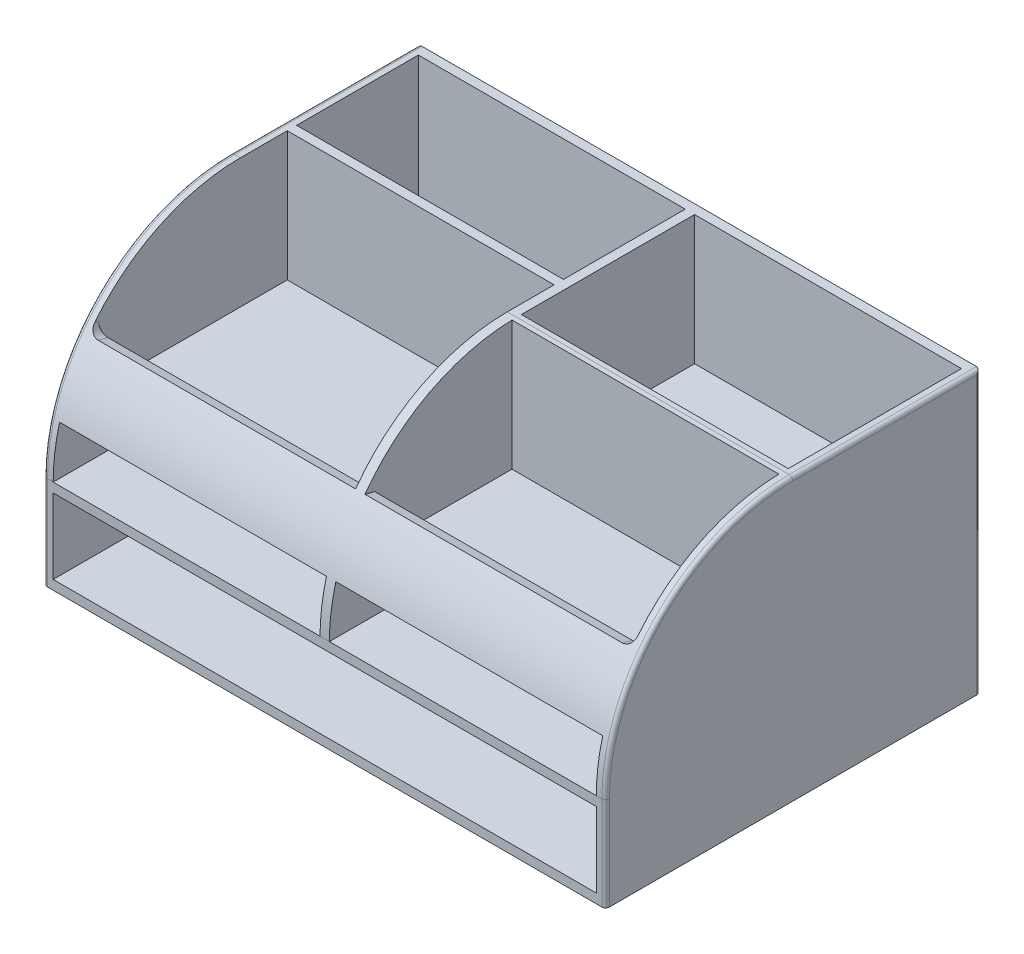
SolidWorks part; units mm, degrees
ref_plane "Front Plane" through (0, 0, 0) normal (0, 0, 1) x (1, 0, 0)
ref_plane "Top Plane" through (0, 0, 0) normal (0, 1, 0) x (1, 0, 0)
ref_plane "Right Plane" through (0, 0, 0) normal (1, 0, 0) x (0, 0, -1)
sketch "Sketch1" plane through (0, 0, 0) normal (1, 0, 0) x (0, 0, -1)
  line L0 (-96.9697, -62.8788) -> (103.0303, -62.8788)
  line L1 (103.0303, -62.8788) -> (103.0303, 87.1212)
  line L2 (103.0303, 87.1212) -> (3.0303, 87.1212)
  line L3 (-96.9697, -12.8788) -> (-96.9697, -62.8788)
  arc A1 (3.0303, 87.1212) -> (-96.9697, -12.8788) centre (3.0303, -12.8788) ccw
  dimension "D3" = 100
  dimension "D1" = 200
  dimension "D2" = 150
extrude "Boss-Extrude1" add sketch "Sketch1" against normal blind 300
sketch "Sketch2" plane through (0, 87.1212, 0) normal (0, 1, 0) x (1, 0, 0)
  line L0 (-300, 103.0303) -> (-300, 3.0303) construction
  line L1 (-295, 98.0303) -> (-5, 98.0303)
  line L2 (-295, 98.0303) -> (-295, -91.9697)
  line L3 (-295, -91.9697) -> (-5, -91.9697)
  line L4 (-5, 98.0303) -> (-5, -91.9697)
  line L5 (-300, 103.0303) -> (0, 103.0303) construction
  line L6 (0, 103.0303) -> (0, 3.0303) construction
  line L7 (-300, -96.9697) -> (0, -96.9697) construction
  line L8 (-295, 33.0303) -> (-152.5, 33.0303)
  line L9 (-150, 98.0303) -> (-150, -91.9697) construction
  line L10 (-152.5, 98.0303) -> (-152.5, -91.9697)
  line L11 (-147.5, 98.0303) -> (-147.5, -91.9697)
  line L12 (-295, 28.0303) -> (-152.5, 28.0303)
  line L13 (-300, 3.0303) -> (0, 3.0303) construction
  line L14 (-300, 3.0303) -> (0, 3.0303) construction
  line L15 (-300, 0.5303) -> (0, 0.5303)
  line L16 (-300, 5.5303) -> (0, 5.5303)
  line M11 (-300, 3.0303) -> (0, 3.0303)
  dimension "D1" = 5
  dimension "D2" = 5
  dimension "D3" = 5
  dimension "D4" = 5
  dimension "D7" = 65
  dimension "D5" = 2.5
  dimension "D6" = 2.5
  dimension "D8" = 5
  dimension "D9" = 2.5
  dimension "D10" = 2.5
extrude "Cut-Extrude1" cut sketch "Sketch2" against normal blind 69 contours L10 L1 L2 L8 | L11 L16 L4 L1 | L15 L11 L3 L4 | L15 L2 L3 L10 | L2 L16 L10 L12 | L16 L2 L10 M11 | L2 L15 L10 M11
sketch "Sketch3" plane through (0, 0, 96.9697) normal (0, 0, 1) x (1, 0, 0)
  line L0 (-5, -17.8788) -> (-295, -17.8788)
  line L1 (-295, -17.8788) -> (-295, -57.8788)
  line L2 (-295, -57.8788) -> (-5, -57.8788)
  line L3 (-5, -57.8788) -> (-5, -17.8788)
  line L4 (0, -62.8788) -> (0, -12.8788)
  line L5 (0, -12.8788) -> (-300, -12.8788)
  line L6 (-300, -12.8788) -> (-300, -62.8788)
  line L7 (-300, -62.8788) -> (0, -62.8788)
  line L8 (0, -62.8788) -> (0, -12.8788) construction
  line L9 (0, -12.8788) -> (-300, -12.8788) construction
  line L10 (-300, -12.8788) -> (-300, -62.8788) construction
  line L11 (-300, -62.8788) -> (0, -62.8788) construction
  line L13 (-295, 13.1212) -> (-5, 13.1212)
  line L14 (-295, 13.1212) -> (-295, -12.8788)
  line L15 (-295, -12.8788) -> (-5, -12.8788)
  line L16 (-5, 13.1212) -> (-5, -12.8788)
  line L17 (-152.5, 18.1212) -> (-152.5, 87.1212) construction
  line L18 (-152.5, -12.8788) -> (-152.5, 87.1212)
  line L19 (-147.5, 18.1212) -> (-147.5, 87.09) construction
  line L20 (-147.5, -12.8788) -> (-147.5, 87.09)
  line L21 (-295, 18.1212) -> (-152.5, 18.1212) construction
  line M10 (0, -12.8788) -> (-300, -12.8788)
  dimension "D3" = 5
  dimension "D1" = 0
  dimension "D2" = 5
extrude "Cut-Extrude2" cut sketch "Sketch3" against normal blind 195 contours L20 L16 L13 M10 | L15 L18 L13 L14 | L2 L3 L0 L1
sketch "Sketch4" plane through (-295, 0, 0) normal (1, 0, 0) x (0, 0, -1)
  line L0 (28.0303, 18.1212) -> (-77.9833, 45.7453)
  line L1 (-72.7698, 44.3868) -> (-72.7698, 18.1212)
  line L2 (-91.9697, 18.1212) -> (-72.7698, 18.1212)
  line L4 (-91.9697, 18.3462) -> (-91.9697, 18.1212)
  line L5 (-91.9697, 18.1212) -> (28.0303, 18.1212)
  line L6 (28.0303, 18.1212) -> (28.0303, 87.1212)
  line L7 (28.0303, 87.1212) -> (3.0303, 87.1212)
  line L8 (-91.9697, 18.3462) -> (-91.9697, 18.1212)
  line L9 (-91.9697, 18.1212) -> (28.0303, 18.1212)
  line L10 (28.0303, 18.1212) -> (28.0303, 87.1212)
  line L11 (28.0303, 87.1212) -> (3.0303, 87.1212)
  arc A0 (3.0303, 82.1212) -> (-87.2197, 16.785) centre (3.0303, -12.8788) ccw
  arc A1 (3.0303, 87.1212) -> (-91.9697, 18.3462) centre (3.0303, -12.8788) ccw
  arc A2 (3.0303, 87.1212) -> (-91.9697, 18.3462) centre (3.0303, -12.8788) ccw
  point P9 (-72.7698, 44.3868)
  arc M9 (3.0303, 87.1212) -> (-91.9697, 18.3462) centre (3.0303, -12.8788) ccw
  line M10 (-91.9697, 18.3462) -> (-91.9697, 18.1212)
  line M11 (-91.9697, 18.1212) -> (28.0303, 18.1212)
  dimension "D1" = 0
  dimension "D2" = 5
extrude "Boss-Extrude2" add sketch "Sketch4" along normal up to surface (290 mm away) contours L1 A0 L9 | A0 L0 M9 M10 M11 up to face at (-5, 39.086, 48.4444)
fillet "Fillet1" radius 2 8 edges at (-300, 87.1212, -53.0303) (-300, -37.8788, 96.9697) (0, 87.1212, -53.0303) (0, -37.8788, 96.9697) (-300, 57.8319, 67.6804) (0, 57.8319, 67.6804) (-300, 12.1212, -103.0303) (0, 12.1212, -103.0303)
fillet "Fillet2" radius 5 2 edges at (-5, 45.0661, 75.3765) (-295, 45.0661, 75.3765)
sketch "Sketch5" plane through (0, 0, 96.9697) normal (0, 0, 1) x (1, 0, 0)
  line L12 (-295, -12.8788) -> (-152.5, -12.8788)
  line L13 (-152.5, -12.8788) -> (-152.5, 13.1212)
  line L14 (-152.5, 13.1212) -> (-295, 13.1212)
  line L15 (-295, 13.1212) -> (-295, -12.8788)
  line L16 (-295, -12.8788) -> (-152.5, -12.8788)
  line L17 (-152.5, -12.8788) -> (-152.5, 13.1212)
  line L18 (-152.5, 13.1212) -> (-295, 13.1212)
  line L19 (-295, 13.1212) -> (-295, -12.8788)
  dimension "D1" = 0
